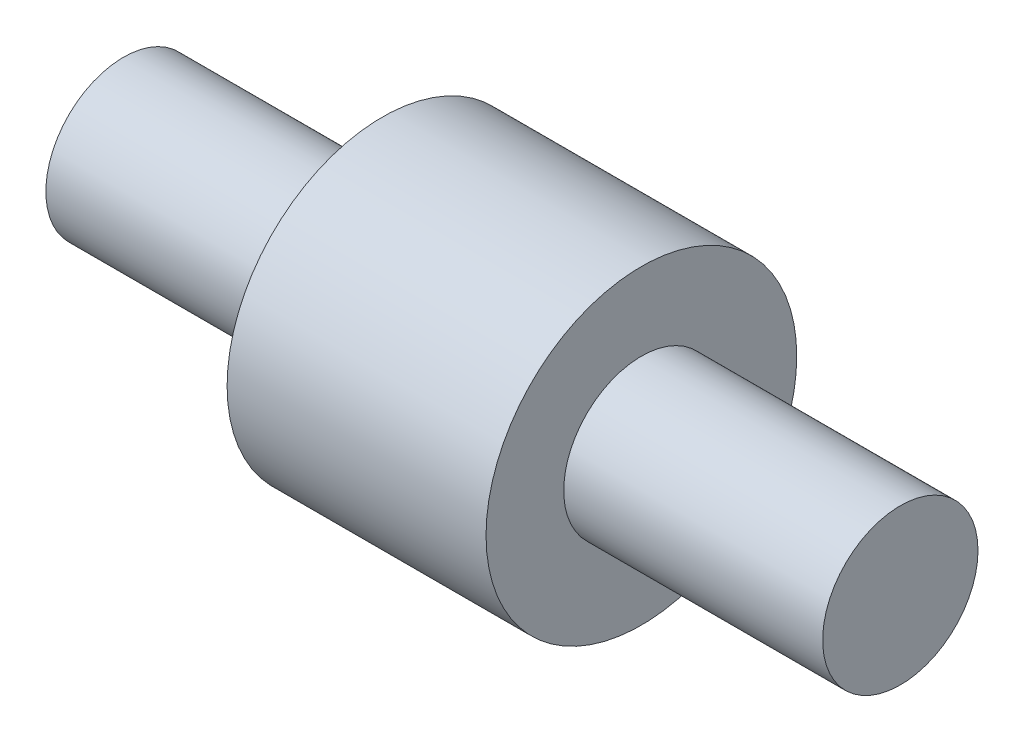
SolidWorks part; units mm, degrees
ref_plane "Plan de face" through (0, 0, 0) normal (0, 0, 1) x (1, 0, 0)
ref_plane "Plan de dessus" through (0, 0, 0) normal (0, 1, 0) x (1, 0, 0)
ref_plane "Plan de droite" through (0, 0, 0) normal (1, 0, 0) x (0, 0, -1)
sketch "Esquisse1" plane through (0, 0, 0) normal (0, 0, 1) x (1, 0, 0)
  line L0 (0, 0) -> (0, 1.5)
  line L1 (0, 1.5) -> (5, 1.5)
  line L2 (5, 1.5) -> (5, 3)
  line L3 (5, 3) -> (10, 3)
  line L4 (10, 3) -> (10, 1.5)
  line L5 (10, 1.5) -> (15, 1.5)
  line L6 (15, 1.5) -> (15, 0)
  line L7 (15, 0) -> (0, 0)
  point P2 (0, 0)
  dimension "D1" = 1.5
  dimension "D2" = 1.5
  dimension "D3" = 3
  dimension "D4" = 5
  dimension "D5" = 5
  dimension "D6" = 5
revolve "Révolution1" add sketch "Esquisse1" angle 360 about L7
